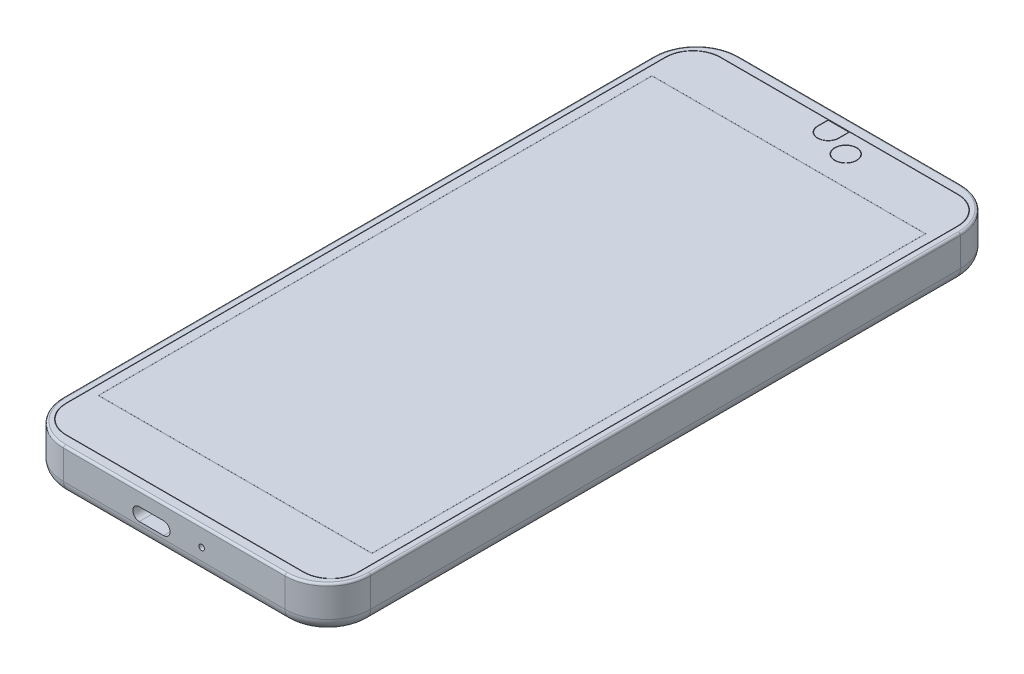
SolidWorks part; units mm, degrees
ref_plane "Ebene vorne" through (0, 0, 0) normal (0, 0, 1) x (1, 0, 0)
ref_plane "Ebene oben" through (0, 0, 0) normal (0, 1, 0) x (1, 0, 0)
ref_plane "Ebene rechts" through (0, 0, 0) normal (1, 0, 0) x (0, 0, -1)
sketch "Skizze1" plane through (0, 0, 0) normal (0, 1, 0) x (1, 0, 0)
  line L1 (-35.9, -79) -> (35.9, -79)
  line L2 (-35.9, -79) -> (-35.9, 79)
  line L3 (-35.9, 79) -> (35.9, 79)
  line L4 (35.9, -79) -> (35.9, 79)
  line L5 (0, 79) -> (0, -79) construction
  line L6 (-35.9, 0) -> (35.9, 0) construction
  point P0 (0, 0)
  dimension "D1" = 71.8
  dimension "D2" = 158
extrude "Aufsatz-Linear austragen1" add sketch "Skizze1" along normal blind 10.25
fillet "Verrundung1" radius 10 4 edges at (-35.9, 5.125, -79) (35.9, 5.125, -79) (-35.9, 5.125, 79) (35.9, 5.125, 79)
fillet "Verrundung2" radius 3 8 edges at (-32.9711, 0, 76.0711) (-35.9, 0, 0) (-32.9711, 0, -76.0711) (0, 0, -79) (32.9711, 0, -76.0711) (35.9, 0, 0) (32.9711, 0, 76.0711) (0, 0, 79)
fillet "Verrundung3" radius 0.5 8 edges at (-32.9711, 10.25, 76.0711) (-35.9, 10.25, 0) (-32.9711, 10.25, -76.0711) (0, 10.25, -79) (32.9711, 10.25, -76.0711) (35.9, 10.25, 0) (32.9711, 10.25, 76.0711) (0, 10.25, 79)
sketch "Skizze2" plane through (0, 10.25, 0) normal (0, 1, 0) x (1, 0, 0)
  line L1 (-27.75, 76.575) -> (27.75, 76.575)
  line L2 (-34.25, 70.075) -> (-34.25, -70.075)
  line L3 (-27.75, -76.575) -> (27.75, -76.575)
  line L4 (34.25, 70.075) -> (34.25, -70.075)
  line L5 (0, -76.575) -> (0, 76.575) construction
  line L6 (-34.25, 0) -> (34.25, 0) construction
  arc A0 (27.75, -76.575) -> (34.25, -70.075) centre (27.75, -70.075) ccw
  arc A1 (-34.25, -70.075) -> (-27.75, -76.575) centre (-27.75, -70.075) ccw
  arc A2 (27.75, 76.575) -> (34.25, 70.075) centre (27.75, 70.075) cw
  arc A3 (-27.75, 76.575) -> (-34.25, 70.075) centre (-27.75, 70.075) ccw
  point P0 (0, 0)
  point P8 (-34.25, -76.575)
  point P14 (-34.25, 76.575)
  dimension "D3" = 6.5
  dimension "D1" = 68.5
  dimension "D2" = 153.15
extrude "Schnitt-Linear-Austragen-Dünn1" cut sketch "Skizze2" against normal blind 0.5 thin
sketch "Skizze3" plane through (0, 10.25, 0) normal (0, 1, 0) x (1, 0, 0)
  line L0 (27.75, 76.475) -> (-27.75, 76.475) construction
  line L1 (-0.01, 71.475) -> (0.01, 71.475)
  line L2 (-2.5, 73.965) -> (-2.5, 76.475)
  line L3 (-2.5, 76.475) -> (2.5, 76.475)
  line L4 (2.5, 73.965) -> (2.5, 76.475)
  line L5 (0, 76.475) -> (0, 71.475) construction
  line L6 (-2.5, 75.22) -> (2.5, 75.22) construction
  arc A0 (0.01, 71.475) -> (2.5, 73.965) centre (0.01, 73.965) ccw
  arc A1 (-0.01, 71.475) -> (-2.5, 73.965) centre (-0.01, 73.965) cw
  point P0 (0, 75.22)
  point P8 (2.5, 71.475)
  point P12 (-2.5, 71.475)
  dimension "D3" = 2.49
  dimension "D1" = 5
  dimension "D2" = 5
extrude "Schnitt-Linear-Austragen-Dünn2" cut sketch "Skizze3" against normal blind 0.5 thin thin type one direction reverse wall 0.1
sketch "Skizze4" plane through (0, 10.25, 0) normal (0, 1, 0) x (1, 0, 0)
  line L0 (27.75, 76.575) -> (-27.75, 76.575) construction
  line L1 (2.5, 73.965) -> (2.5, 76.475) construction
  circle A0 centre (6.5, 71.575) radius 2.5
  dimension "D1" = 5
  dimension "D2" = 5
  dimension "D3" = 4
extrude "Schnitt-Linear-Austragen-Dünn3" cut sketch "Skizze4" against normal blind 0.5 thin
sketch "Skizze5" plane through (-35.9, 0, 0) normal (-1, 0, 0) x (0, 0, 1)
  line L0 (-36.1, 7.25) -> (-33.8, 7.25) construction
  line L1 (-45.7, 4.61) -> (-36.1, 4.61)
  line L2 (-47, 5.91) -> (-47, 5.95)
  line L3 (-45.7, 7.25) -> (-36.1, 7.25)
  line L4 (-36.1, 4.61) -> (-36.1, 7.25)
  line L5 (-40.9, 7.25) -> (-40.9, 4.61) construction
  line L6 (-47, 5.93) -> (-36.1, 5.93) construction
  line L7 (-24.2, 7.25) -> (-33.8, 7.25)
  line L8 (-22.9, 5.95) -> (-22.9, 5.91)
  line L9 (-24.2, 4.61) -> (-33.8, 4.61)
  line L10 (-33.8, 7.25) -> (-33.8, 4.61)
  line L11 (-29, 4.61) -> (-29, 7.25) construction
  line L12 (-22.9, 5.93) -> (-33.8, 5.93) construction
  line L13 (-5.5, 7.25) -> (-13.95, 7.25)
  line L14 (-4.2, 5.95) -> (-4.2, 5.91)
  line L15 (-5.5, 4.61) -> (-13.95, 4.61)
  line L16 (-15.25, 5.95) -> (-15.25, 5.91)
  line L17 (-9.725, 4.61) -> (-9.725, 7.25) construction
  line L18 (-4.2, 5.93) -> (-15.25, 5.93) construction
  line L19 (-22.9, 7.25) -> (-15.25, 7.25) construction
  line L20 (-36.1, 4.61) -> (-33.8, 4.61) construction
  line L21 (-22.9, 4.61) -> (-15.25, 4.61) construction
  line L22 (-69, 10.25) -> (69, 10.25) construction
  line L23 (-79, 3) -> (-79, 9.75) construction
  arc A0 (-4.2, 5.91) -> (-5.5, 4.61) centre (-5.5, 5.91) cw
  arc A1 (-5.5, 7.25) -> (-4.2, 5.95) centre (-5.5, 5.95) cw
  arc A2 (-13.95, 4.61) -> (-15.25, 5.91) centre (-13.95, 5.91) cw
  arc A3 (-13.95, 7.25) -> (-15.25, 5.95) centre (-13.95, 5.95) ccw
  arc A4 (-22.9, 5.91) -> (-24.2, 4.61) centre (-24.2, 5.91) cw
  arc A5 (-24.2, 7.25) -> (-22.9, 5.95) centre (-24.2, 5.95) cw
  arc A6 (-45.7, 4.61) -> (-47, 5.91) centre (-45.7, 5.91) cw
  arc A7 (-47, 5.95) -> (-45.7, 7.25) centre (-45.7, 5.95) cw
  point P0 (-40.9, 5.93)
  point P4 (-29, 5.93)
  point P8 (-9.725, 5.93)
  point P36 (-47, 7.25)
  dimension "D8" = 1.3
  dimension "D1" = 10.9
  dimension "D2" = 11.05
  dimension "D3" = 2.64
  dimension "D4" = 3
  dimension "D5" = 32
  dimension "D6" = 2.3
  dimension "D7" = 7.65
extrude "Aufsatz-Linear austragen2" add sketch "Skizze5" along normal blind 0.5
sketch "Skizze6" plane through (0, 0, -79) normal (0, 0, -1) x (-1, 0, 0)
  line L0 (35.9, 9.75) -> (35.9, 3) construction
  line L1 (25.9, 0) -> (-25.9, 0) construction
  circle A0 centre (23.4, 4.55) radius 1.875
  circle A1 centre (12.4, 6) radius 0.65
  dimension "D1" = 3.75
  dimension "D4" = 1.3
  dimension "D2" = 12.5
  dimension "D3" = 4.55
  dimension "D5" = 6
  dimension "D6" = 23.5
extrude "Schnitt-Linear austragen1" cut sketch "Skizze6" against normal blind 25
sketch "Skizze7" plane through (0, 0, 79) normal (0, 0, 1) x (1, 0, 0)
  line L0 (-8.2, 5.25) -> (-2.5, 5.25) construction
  line L1 (-8.2, 6.75) -> (-2.5, 6.75)
  line L2 (-8.2, 3.75) -> (-2.5, 3.75)
  line L3 (35.9, 9.75) -> (35.9, 3) construction
  line L4 (-25.9, 10.25) -> (25.9, 10.25) construction
  line L6 (25.9, 0) -> (-25.9, 0) construction
  circle A0 centre (6.4, 5.8) radius 0.65
  arc A1 (-8.2, 6.75) -> (-8.2, 3.75) centre (-8.2, 5.25) ccw
  arc A2 (-2.5, 3.75) -> (-2.5, 6.75) centre (-2.5, 5.25) ccw
  point P4 (-5.35, 5.25)
  point P9 (-9.7, 5.25)
  point P10 (-1, 5.25)
  dimension "D1" = 1.3
  dimension "D3" = 8.7
  dimension "D2" = 3
  dimension "D4" = 36.9
  dimension "D5" = 3.5
  dimension "D6" = 5.8
  dimension "D7" = 29.5
extrude "Schnitt-Linear austragen2" cut sketch "Skizze7" against normal blind 7
sketch "Skizze8" plane through (0, 0, 0) normal (0, -1, 0) x (1, 0, 0)
  line L0 (25.9, -79) -> (-22.345, -79) construction
  circle A0 centre (0, -55.5) radius 5.25
  dimension "D1" = 10.5
  dimension "D2" = 23.5
extrude "Schnitt-Linear austragen3" cut sketch "Skizze8" against normal blind 0.9
chamfer "Fase1" distance 0.8 angle 45 1 edges at (0, 0, -60.75)
sketch "Skizze9" plane through (0, 0, 0) normal (0, -1, 0) x (1, 0, 0)
  line L0 (25.4, -69) -> (16.5, -69) construction
  line L1 (25.4, -74.5) -> (16.5, -74.5)
  line L2 (25.4, -63.5) -> (16.5, -63.5)
  line L3 (25.9, -79) -> (-22.345, -79) construction
  line L4 (35.9, 69) -> (35.9, -69) construction
  arc A0 (25.4, -74.5) -> (25.4, -63.5) centre (25.4, -69) ccw
  arc A1 (16.5, -63.5) -> (16.5, -74.5) centre (16.5, -69) ccw
  point P2 (20.95, -69)
  point P7 (30.9, -69)
  point P8 (11, -69)
  dimension "D1" = 11
  dimension "D2" = 19.9
  dimension "D3" = 4.5
  dimension "D4" = 5
extrude "Schnitt-Linear austragen4" cut sketch "Skizze9" against normal blind 0.3
chamfer "Fase2" distance 0.2 angle 45 4 edges at (20.95, 0, -74.5) (30.9, 0, -69) (11, 0, -69) (20.95, 0, -63.5)
sketch "Skizze10" plane through (0, 10.25, 0) normal (0, 1, 0) x (1, 0, 0)
  line L1 (-31.94, -64.7) -> (31.94, -64.7)
  line L2 (-31.94, -64.7) -> (-31.94, 64.7)
  line L3 (-31.94, 64.7) -> (31.94, 64.7)
  line L4 (31.94, -64.7) -> (31.94, 64.7)
  line L5 (0, 64.7) -> (0, -64.7) construction
  line L6 (-31.94, 0) -> (31.94, 0) construction
  point P0 (0, 0)
  point P4 (0, 0)
  dimension "D1" = 63.88
  dimension "D2" = 129.4
extrude "Schnitt-Linear-Austragen-Dünn4" cut sketch "Skizze10" against normal blind 0.01 thin
sketch "Skizze11" plane through (-35.9, 0, 0) normal (-1, 0, 0) x (0, 0, 1)
  line L0 (56.1, 5.35) -> (60.9, 5.35) construction
  line L1 (56.1, 6.25) -> (60.9, 6.25)
  line L2 (56.1, 4.45) -> (60.9, 4.45)
  line L3 (63.55, 5.35) -> (68.35, 5.35) construction
  line L4 (63.55, 6.25) -> (68.35, 6.25)
  line L5 (63.55, 4.45) -> (68.35, 4.45)
  line L6 (79, 9.75) -> (79, 3) construction
  line L7 (-69, 10.25) -> (69, 10.25) construction
  line L8 (41.55, 3) -> (48.9, 3) construction
  line L9 (-69, 3) -> (69, 3) construction
  line L10 (41.55, 4.3) -> (48.9, 4.3) construction
  line L11 (41.55, 1.7) -> (48.9, 1.7) construction
  line L12 (41.55, 4.3) -> (48.9, 4.3)
  line L13 (40.25, 3) -> (40.7696, 2.7)
  line L14 (40.7696, 2.7) -> (49.6804, 2.7)
  line L15 (49.6804, 2.7) -> (50.2, 3)
  arc A0 (56.1, 6.25) -> (56.1, 4.45) centre (56.1, 5.35) ccw
  arc A1 (60.9, 4.45) -> (60.9, 6.25) centre (60.9, 5.35) ccw
  arc A2 (63.55, 6.25) -> (63.55, 4.45) centre (63.55, 5.35) ccw
  arc A3 (68.35, 4.45) -> (68.35, 6.25) centre (68.35, 5.35) ccw
  arc A4 (41.55, 4.3) -> (41.55, 1.7) centre (41.55, 3) ccw construction
  arc A5 (48.9, 1.7) -> (48.9, 4.3) centre (48.9, 3) ccw construction
  arc A6 (40.25, 3) -> (41.55, 4.3) centre (41.55, 3) cw
  arc A7 (50.2, 3) -> (48.9, 4.3) centre (48.9, 3) ccw
  point P2 (58.5, 5.35)
  point P7 (65.95, 5.35)
  point P14 (55.2, 5.35)
  point P15 (61.8, 5.35)
  point P16 (62.65, 5.35)
  point P17 (69.25, 5.35)
  point P26 (45.225, 3)
  point P32 (40.25, 3)
  point P33 (50.2, 3)
  point P37 (40.6543, 2.7)
  point P39 (49.5873, 2.7)
  point P40 (0, 0)
  dimension "D7" = 9.95
  dimension "D1" = 1.8
  dimension "D2" = 6.6
  dimension "D3" = 0.85
  dimension "D4" = 9.75
  dimension "D5" = 4
  dimension "D6" = 1.3
  dimension "D8" = 5
  dimension "D9" = 0.3
  dimension "D10" = 30
extrude "Schnitt-Linear austragen5" cut sketch "Skizze11" against normal blind 2
